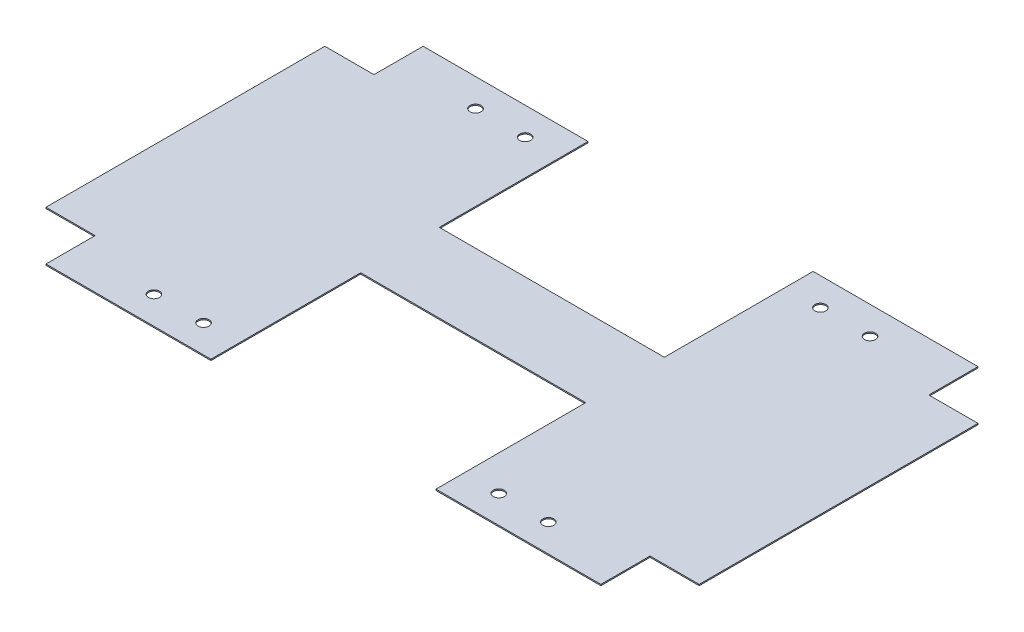
SolidWorks part; units mm, degrees
ref_plane "Front Plane" through (0, 0, 0) normal (0, 0, 1) x (1, 0, 0)
ref_plane "Top Plane" through (0, 0, 0) normal (0, 1, 0) x (1, 0, 0)
ref_plane "Right Plane" through (0, 0, 0) normal (1, 0, 0) x (0, 0, -1)
sketch "Sketch1" plane through (0, 0, 0) normal (0, 1, 0) x (1, 0, 0)
  line L0 (-22.9, 38.37) -> (-22.9, 8.105)
  line L1 (-56.46, 38.37) -> (-22.9, 38.37)
  line L2 (-66.46, 28.37) -> (-66.46, -28.37)
  line L3 (-56.46, -38.37) -> (-22.9, -38.37)
  line L4 (66.46, 28.37) -> (66.46, -28.37)
  line L5 (-66.46, 38.37) -> (66.46, -38.37) construction
  line L6 (-66.46, -38.37) -> (66.46, 38.37) construction
  line L7 (-22.9, 8.105) -> (22.9, 8.105)
  line L8 (22.9, 8.105) -> (22.9, 38.37)
  line L9 (22.9, -7.895) -> (22.9, -38.37)
  line L10 (-22.9, -38.37) -> (-22.9, -7.895)
  line L11 (-22.9, -7.895) -> (22.9, -7.895)
  line L12 (0, 8.105) -> (0, -7.895) construction
  line L13 (22.9, 38.37) -> (56.46, 38.37)
  line L14 (22.9, -38.37) -> (56.46, -38.37)
  line L15 (-66.46, -28.37) -> (-56.46, -28.37)
  line L16 (-56.46, -28.37) -> (-56.46, -38.37)
  line L17 (66.46, -28.37) -> (56.46, -28.37)
  line L18 (56.46, -28.37) -> (56.46, -38.37)
  line L19 (66.46, 28.37) -> (56.46, 28.37)
  line L20 (56.46, 28.37) -> (56.46, 38.37)
  line L21 (-56.46, 38.37) -> (-56.46, 28.37)
  line L22 (-56.46, 28.37) -> (-66.46, 28.37)
  circle A0 centre (-40.14, 32.72) radius 1.125
  circle A1 centre (-30.04, 32.72) radius 1.125
  circle A2 centre (30.04, 32.72) radius 1.125
  circle A3 centre (40.14, 32.72) radius 1.125
  circle A4 centre (40.14, -32.73) radius 1.125
  circle A5 centre (30.04, -32.73) radius 1.125
  circle A6 centre (-30.04, -32.73) radius 1.125
  circle A7 centre (-40.14, -32.73) radius 1.125
  point P0 (0, 0)
  dimension "D9" = 2.25
  dimension "D1" = 132.92
  dimension "D2" = 30.475
  dimension "D3" = 16
  dimension "D4" = 45.8
  dimension "D5" = 10
  dimension "D6" = 10
  dimension "D7" = 10
  dimension "D8" = 10
  dimension "D10" = 10.1
  dimension "D11" = 10.1
  dimension "D12" = 5.65
  dimension "D13" = 5.64
  dimension "D14" = 7.14
  dimension "D15" = 7.14
  dimension "D16" = 30.265
extrude "Boss-Extrude1" add sketch "Sketch1" along normal blind 0.25
